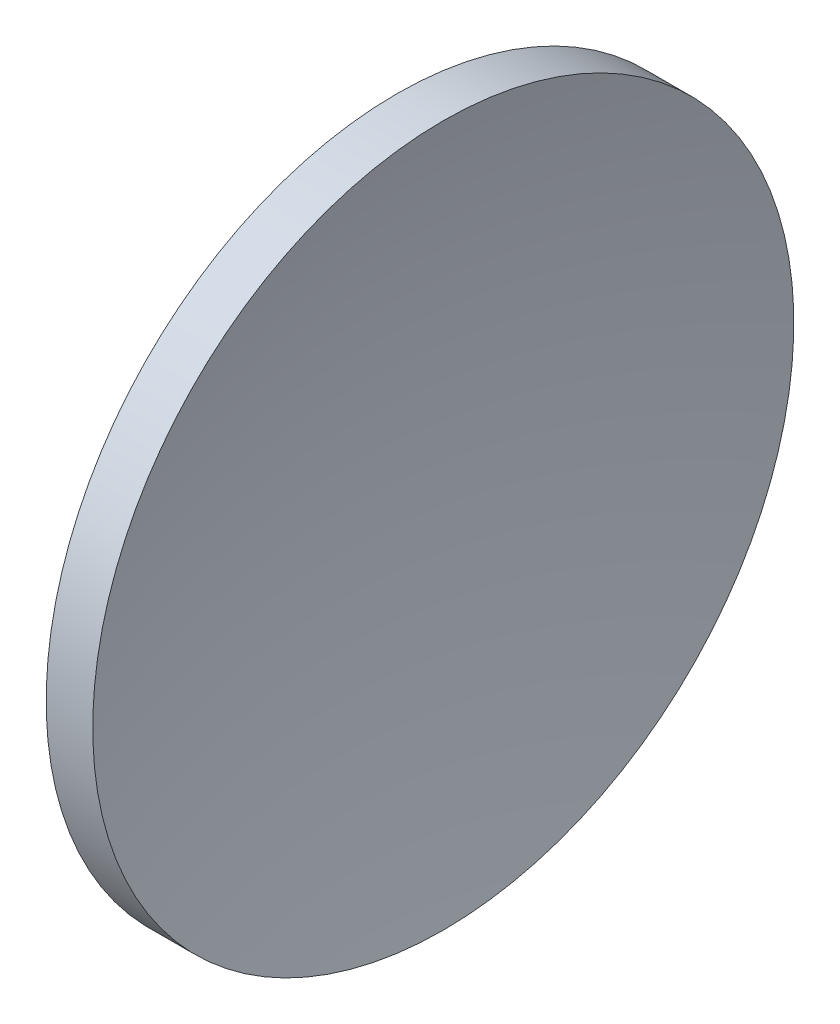
SolidWorks part; units mm, degrees
ref_plane "前视基准面" through (0, 0, 0) normal (0, 0, 1) x (1, 0, 0)
ref_plane "上视基准面" through (0, 0, 0) normal (0, 1, 0) x (1, 0, 0)
ref_plane "右视基准面" through (0, 0, 0) normal (1, 0, 0) x (0, 0, -1)
sketch "草图1" plane through (0, 0, 0) normal (0, 0, 1) x (1, 0, 0)
  line L0 (115.9445, 65.2168) -> (135.9482, 65.2168) construction
  line L1 (125.0268, 77.7168) -> (126.6872, 77.7168)
  line L2 (122.5995, 65.2168) -> (125.0995, 65.2168)
  arc A0 (125.0268, 77.7168) -> (122.5995, 65.2168) centre (155.9995, 65.2168) ccw
  arc A1 (126.6872, 77.7168) -> (125.0995, 65.2168) centre (175.0995, 65.2168) ccw
revolve "旋转1" add sketch "草图1" angle 360 about L0
